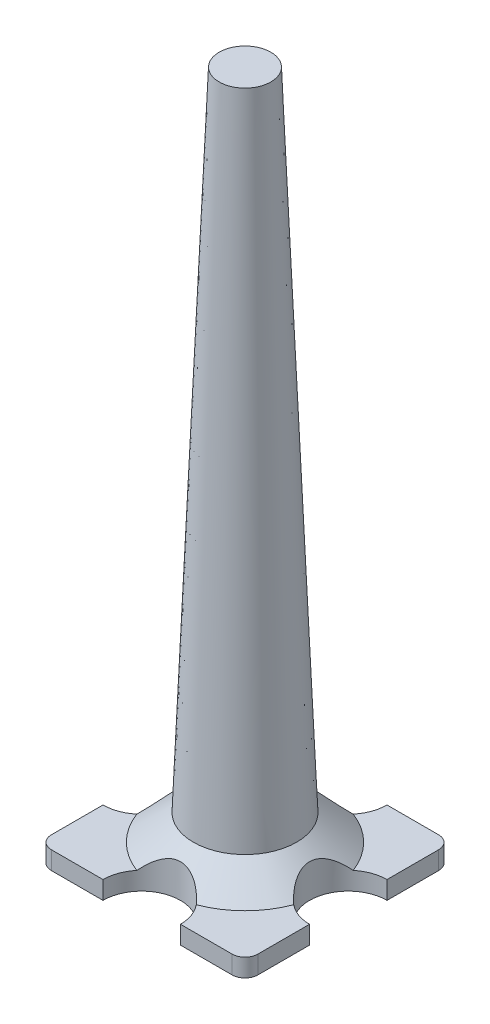
SolidWorks part; units mm, degrees
ref_plane "Front Plane" through (0, 0, 0) normal (0, 0, 1) x (1, 0, 0)
ref_plane "Top Plane" through (0, 0, 0) normal (0, 1, 0) x (1, 0, 0)
ref_plane "Right Plane" through (0, 0, 0) normal (1, 0, 0) x (0, 0, -1)
sketch "Sketch1" plane through (0, 0, 0) normal (0, 1, 0) x (1, 0, 0)
  line L1 (44.45, -50.8) -> (-44.45, -50.8)
  line L2 (50.8, -44.45) -> (50.8, 44.45)
  line L3 (44.45, 50.8) -> (-44.45, 50.8)
  line L4 (-50.8, -44.45) -> (-50.8, 44.45)
  line L5 (50.8, -50.8) -> (-50.8, 50.8) construction
  line L6 (50.8, 50.8) -> (-50.8, -50.8) construction
  arc A0 (50.8, 44.45) -> (44.45, 50.8) centre (44.45, 44.45) ccw
  arc A1 (44.45, -50.8) -> (50.8, -44.45) centre (44.45, -44.45) ccw
  arc A2 (-44.45, -50.8) -> (-50.8, -44.45) centre (-44.45, -44.45) cw
  arc A3 (-44.45, 50.8) -> (-50.8, 44.45) centre (-44.45, 44.45) ccw
  point P0 (0, 0)
  dimension "D2" = 6.35
  dimension "D1" = 101.6
extrude "Boss-Extrude1" add sketch "Sketch1" along normal blind 8.89
sketch "Sketch2" plane through (0, 0, 0) normal (0, 0, 1) x (1, 0, 0)
  line L0 (0, 8.89) -> (0, 21.59)
  line L1 (-44.45, 8.89) -> (44.45, 8.89) construction
  line L2 (0, 21.59) -> (25.4, 21.59)
  line L3 (25.4, 21.59) -> (41.275, 8.89)
  line L4 (0, 37.9719) -> (0, 8.89) construction
  line L5 (-44.45, 0) -> (44.45, 0) construction
  line L6 (0, 8.89) -> (41.275, 8.89)
  dimension "D1" = 21.59
  dimension "D2" = 50.8
  dimension "D3" = 82.55
revolve "Revolve1" add sketch "Sketch2" angle 360 about L4
ref_plane "Plane2" through (0, 21.59, 0) normal (0, 1, 0) x (1, 0, 0)
sketch "Sketch5" plane through (0, 21.59, 0) normal (0, 1, 0) x (1, 0, 0)
  line L0 (44.45, 50.8) -> (-44.45, 50.8) construction
  line L1 (50.8, -44.45) -> (50.8, 44.45) construction
  line L2 (-44.45, -50.8) -> (44.45, -50.8) construction
  line L3 (-50.8, 44.45) -> (-50.8, -44.45) construction
  circle A0 centre (0, 0) radius 19.05
  circle A1 centre (0, 50.8) radius 19.05
  circle A2 centre (50.8, 0) radius 19.05
  circle A3 centre (0, -50.8) radius 19.05
  circle A4 centre (-50.8, 0) radius 19.05
  dimension "D1" = 38.1
  dimension "D2" = 38.1
extrude "Cut-Extrude2" cut sketch "Sketch5" against normal through all contours A3 | A2 | A1 | A4
sketch "Sketch6" plane through (0, 0, 0) normal (0, 0, 1) x (1, 0, 0)
  line L0 (0, 0) -> (0, 512.9369) construction
  line L1 (0, 21.59) -> (25.4, 21.59)
  line L2 (25.4, 21.59) -> (-25.4, 21.59) construction
  line L3 (25.4, 21.59) -> (12.7, 339.09)
  line L4 (12.7, 339.09) -> (0, 339.09)
  line L5 (0, 21.59) -> (0, 339.09)
  dimension "D1" = 25.4
  dimension "D2" = 317.5
revolve "Revolve2" add sketch "Sketch6" angle 360 about L0
